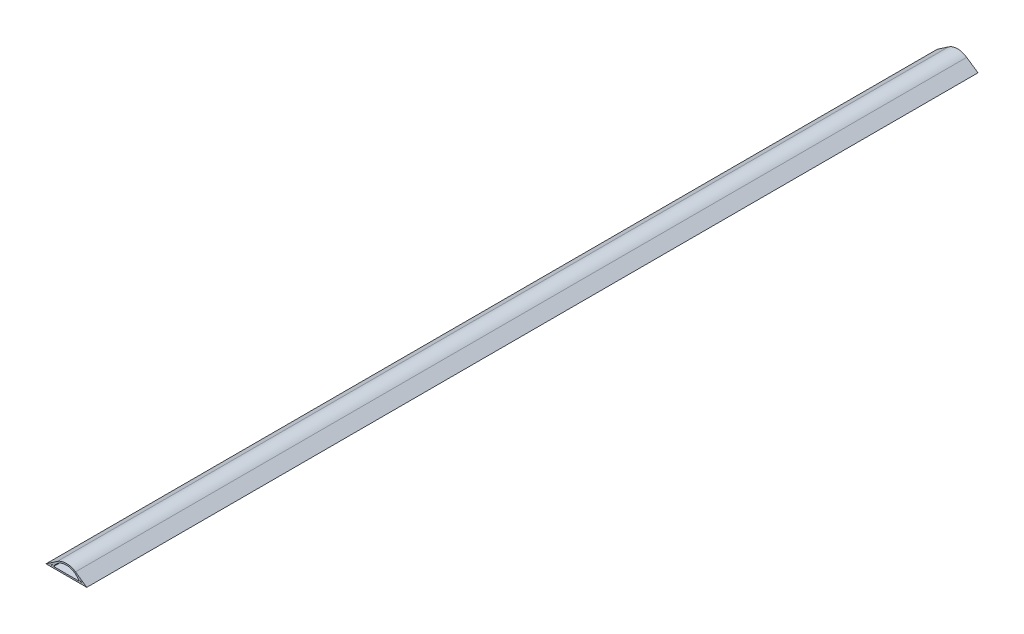
SolidWorks part; units mm, degrees
material "PUR"
ref_plane "Front Plane" through (0, 0, 0) normal (0, 0, 1) x (1, 0, 0)
ref_plane "Top Plane" through (0, 0, 0) normal (0, 1, 0) x (1, 0, 0)
ref_plane "Right Plane" through (0, 0, 0) normal (1, 0, 0) x (0, 0, -1)
sketch "Sketch2" plane through (0, 0, 0) normal (0, 0, 1) x (1, 0, 0)
  line L0 (0, 0) -> (68.58, 0)
  line L1 (34.29, 0) -> (34.29, 17.78) construction
  line L2 (18.9927, 13.0354) -> (0, 0)
  line L3 (49.5873, 13.0354) -> (68.58, 0)
  line L4 (10.9978, 4.4675) -> (8.1894, 2.54)
  line L5 (8.1894, 2.54) -> (9.965, 2.54)
  line L6 (57.5822, 4.4675) -> (60.3906, 2.54)
  line L7 (20.43, 10.9412) -> (8.1894, 2.54) construction
  line L8 (48.15, 10.9412) -> (60.3906, 2.54) construction
  line L9 (12.8231, 2.54) -> (55.7569, 2.54)
  line L10 (8.1894, 2.54) -> (60.3906, 2.54) construction
  line L11 (58.615, 2.54) -> (60.3906, 2.54)
  arc A0 (58.615, 2.54) -> (57.5822, 4.4675) centre (34.29, -9.2529) ccw
  arc A1 (55.7569, 2.54) -> (12.8231, 2.54) centre (34.29, -9.2529) ccw
  circle A2 centre (34.29, -9.2529) radius 27.0329 construction
  circle A3 centre (34.29, -9.2529) radius 24.4929 construction
  arc A4 (10.9978, 4.4675) -> (9.965, 2.54) centre (34.29, -9.2529) ccw
  arc A5 (49.5873, 13.0354) -> (18.9927, 13.0354) centre (34.29, -9.2529) ccw
  point P7 (59.69, 0)
  dimension "D1" = 68.58
  dimension "D2" = 17.78
  dimension "D3" = 8.89
  dimension "D4" = 2.54
  dimension "D5" = 2.54
extrude "Boss-Extrude1" add sketch "Sketch2" along normal blind 1498.6
